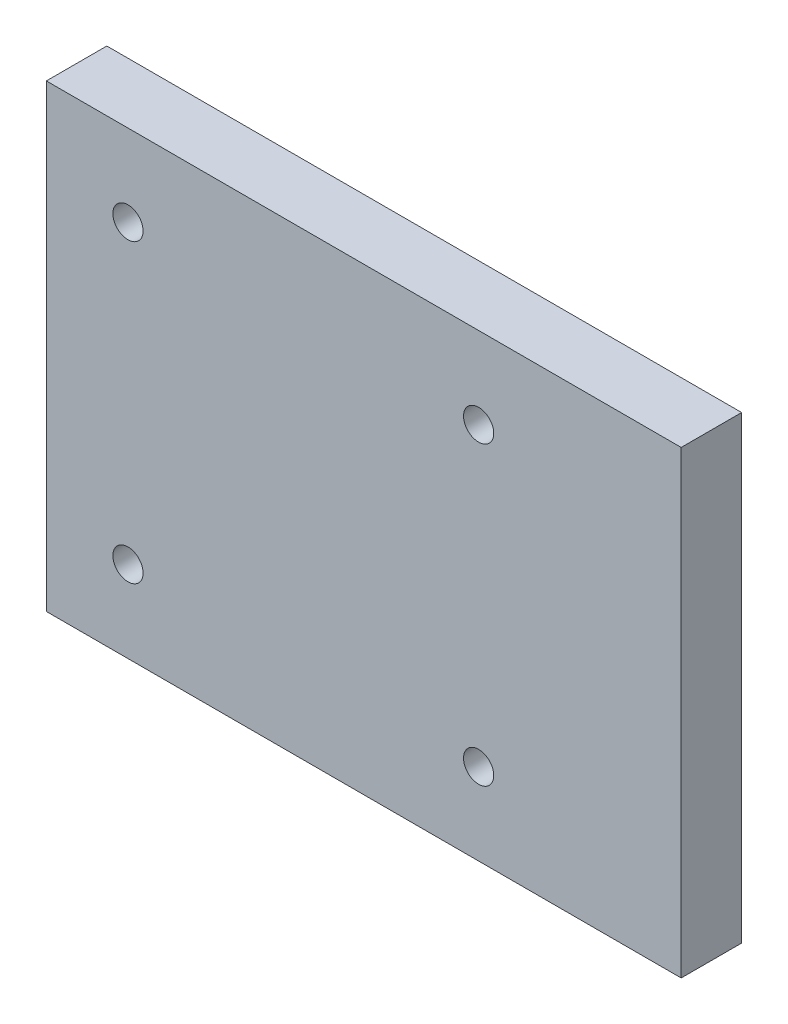
SolidWorks part; units mm, degrees
ref_plane "Front Plane" through (0, 0, 0) normal (0, 0, 1) x (1, 0, 0)
ref_plane "Top Plane" through (0, 0, 0) normal (0, 1, 0) x (1, 0, 0)
ref_plane "Right Plane" through (0, 0, 0) normal (1, 0, 0) x (0, 0, -1)
sketch "Sketch1" plane through (0, 0, 0) normal (0, 0, 1) x (1, 0, 0)
  line L0 (-39.5, -28) -> (39.5, -28) construction
  line L1 (42.5, 28) -> (-42.5, 28)
  line L2 (42.5, 28) -> (42.5, -28)
  line L3 (42.5, -28) -> (-42.5, -28)
  line L4 (-42.5, 28) -> (-42.5, -28)
  line L5 (42.5, -25) -> (42.5, 25) construction
  line L6 (39.5, 28) -> (-39.5, 28) construction
  line L7 (-42.5, 25) -> (-42.5, -25) construction
  line L8 (52.5, 38) -> (52.5, -38)
  line L9 (52.5, -38) -> (-52.5, -38)
  line L10 (-52.5, 38) -> (-52.5, -38)
  line L11 (52.5, 38) -> (-52.5, 38)
  circle A0 centre (19, 24.5) radius 2.5
  circle A1 centre (-39, 24.5) radius 2.5
  circle A2 centre (19, -24.5) radius 2.5
  circle A3 centre (-39, -24.5) radius 2.5
  point P12 (19, 24.5)
  point P13 (-39, 24.5)
  point P15 (19, -24.5)
  point P17 (-39, -24.5)
  dimension "D1" = 5
  dimension "D2" = 10
extrude "Boss-Extrude1" add sketch "Sketch1" along normal blind 10 contours L8 L11 L10 L9 L4 L1 L2 L3 | L1 L4 L3 L2 A3 A2 A1 A0
